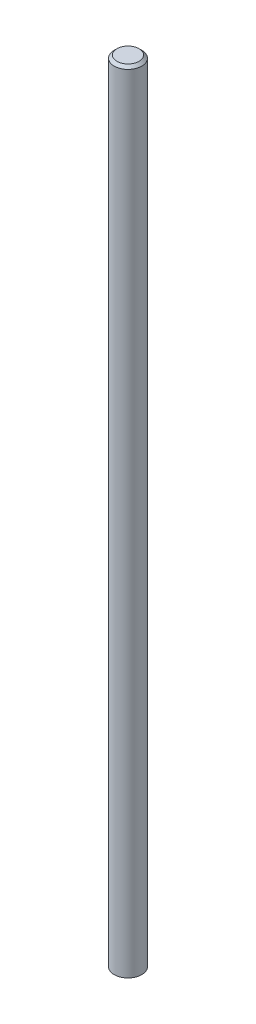
SolidWorks part; units mm, degrees
ref_plane "Front Plane" through (0, 0, 0) normal (0, 0, 1) x (1, 0, 0)
ref_plane "Top Plane" through (0, 0, 0) normal (0, 1, 0) x (1, 0, 0)
ref_plane "Right Plane" through (0, 0, 0) normal (1, 0, 0) x (0, 0, -1)
sketch "Sketch1" plane through (0, 0, 0) normal (0, 1, 0) x (1, 0, 0)
  circle A0 centre (0, 0) radius 1.5
  dimension "D1" = 3
extrude "Boss-Extrude1" add sketch "Sketch1" along normal blind 86
chamfer "Chamfer1" distance 0.3 angle 45 1 edges at (0, 86, 1.5)
